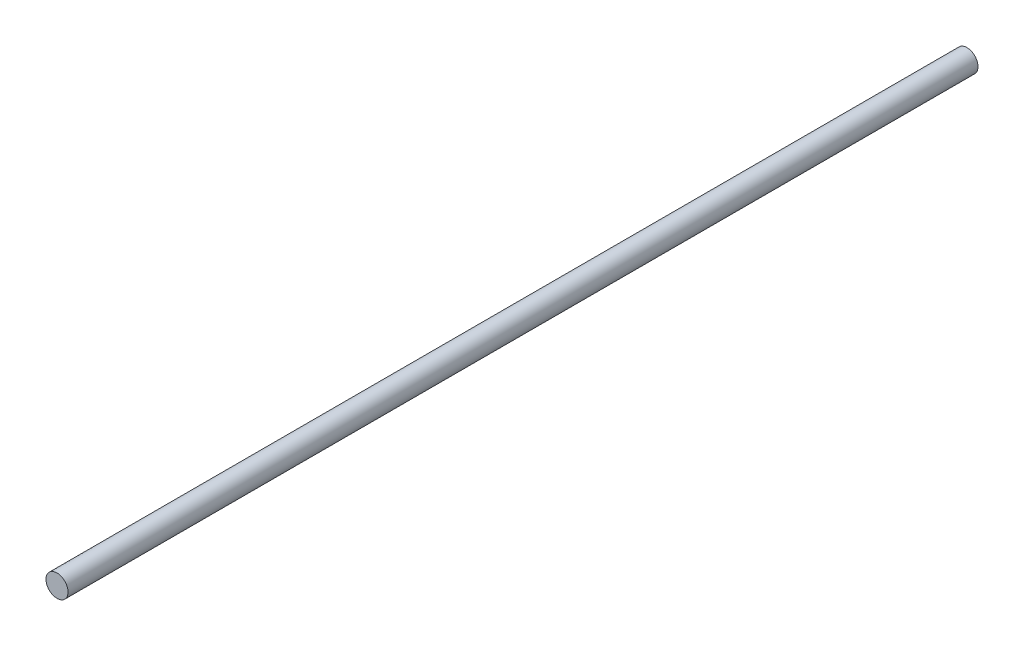
SolidWorks part; units mm, degrees
ref_plane "Front Plane" through (0, 0, 0) normal (0, 0, 1) x (1, 0, 0)
ref_plane "Top Plane" through (0, 0, 0) normal (0, 1, 0) x (1, 0, 0)
ref_plane "Right Plane" through (0, 0, 0) normal (1, 0, 0) x (0, 0, -1)
sketch "Sketch1" plane through (0, 0, 0) normal (0, 0, 1) x (1, 0, 0)
  circle A0 centre (0, 0) radius 4
  dimension "D1" = 8
extrude "Boss-Extrude1" add sketch "Sketch1" along normal blind 330
